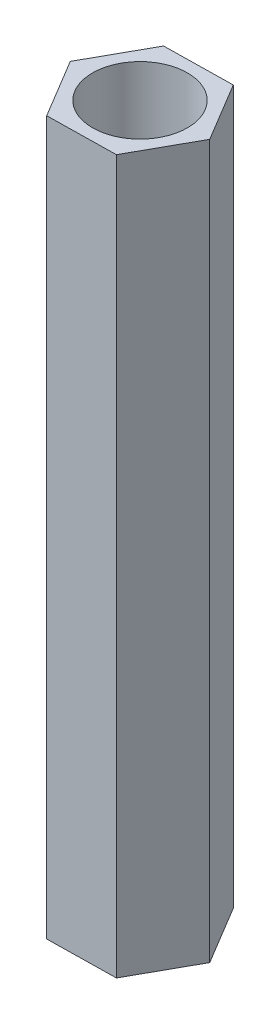
SolidWorks part; units mm, degrees
material "黄铜"
ref_plane "前视基准面" through (0, 0, 0) normal (0, 0, 1) x (1, 0, 0)
ref_plane "上视基准面" through (0, 0, 0) normal (0, 1, 0) x (1, 0, 0)
ref_plane "右视基准面" through (0, 0, 0) normal (1, 0, 0) x (0, 0, -1)
sketch "草图1" plane through (0, 0, 0) normal (0, 1, 0) x (1, 0, 0)
  line L1 (1.4019, 2.5235) -> (-1.4844, 2.4758)
  line L2 (-1.4844, 2.4758) -> (-2.8864, -0.0476)
  line L3 (-2.8864, -0.0476) -> (-1.4019, -2.5235)
  line L4 (-1.4019, -2.5235) -> (1.4844, -2.4758)
  line L5 (1.4844, -2.4758) -> (2.8864, 0.0476)
  line L6 (2.8864, 0.0476) -> (1.4019, 2.5235)
  circle A0 centre (0, 0) radius 2.5 construction
  circle A1 centre (0, 0) radius 2
extrude "凸台-拉伸1" add sketch "草图1" along normal blind 30
